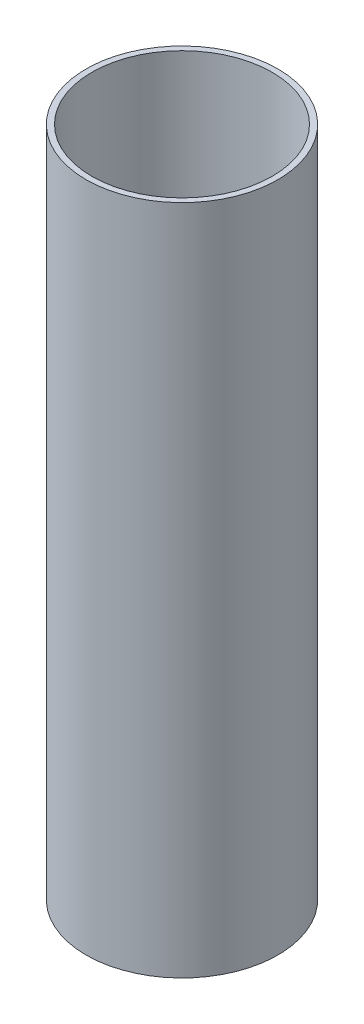
SolidWorks part; units mm, degrees
ref_plane "Front Plane" through (0, 0, 0) normal (0, 0, 1) x (1, 0, 0)
ref_plane "Top Plane" through (0, 0, 0) normal (0, 1, 0) x (1, 0, 0)
ref_plane "Right Plane" through (0, 0, 0) normal (1, 0, 0) x (0, 0, -1)
sketch "Sketch1" plane through (0, 0, 0) normal (0, 1, 0) x (1, 0, 0)
  circle A0 centre (0, 0) radius 6.35
  circle A1 centre (0, 0) radius 5.969
  dimension "D1" = 12.7
  dimension "D2" = 11.938
extrude "Boss-Extrude1" add sketch "Sketch1" along normal blind 44.45
